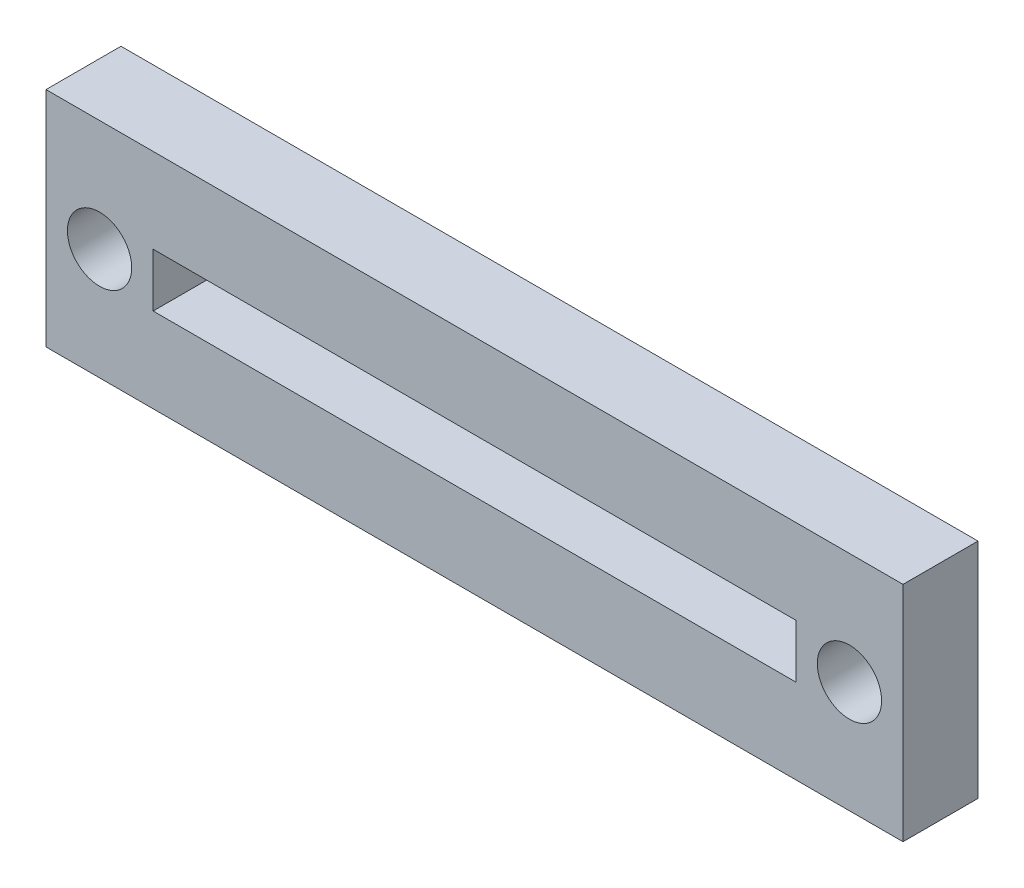
SolidWorks part; units mm, degrees
material "ABS"
ref_plane "Front Plane" through (0, 0, 0) normal (0, 0, 1) x (1, 0, 0)
ref_plane "Top Plane" through (0, 0, 0) normal (0, 1, 0) x (1, 0, 0)
ref_plane "Right Plane" through (0, 0, 0) normal (1, 0, 0) x (0, 0, -1)
sketch "Sketch1" plane through (0, 0, 0) normal (0, 0, -1) x (-1, 0, 0)
  line L0 (20, -1.25) -> (20, -5) construction
  line L1 (5, -1.25) -> (35, -1.25)
  line L2 (5, -1.25) -> (5, 1.25)
  line L3 (5, 1.25) -> (35, 1.25)
  line L4 (35, -1.25) -> (35, 1.25)
  line L6 (20, 1.25) -> (20, 5) construction
  line L7 (40, -5.2021) -> (0, -5.2021)
  line L8 (5, 0) -> (0, 0) construction
  line L9 (40, -5.2021) -> (40, 5.2021)
  line L10 (35, 0) -> (40, 0) construction
  line L11 (40, 5.2021) -> (0, 5.2021)
  line L16 (0, -5.2021) -> (0, 5.2021)
  circle A0 centre (2.5, 0) radius 1.5
  circle A1 centre (37.5, 0) radius 1.5
  dimension "D2" = 3
  dimension "D1" = 30
  dimension "D3" = 2.5
extrude "Boss-Extrude1" add sketch "Sketch1" along normal blind 3.5
